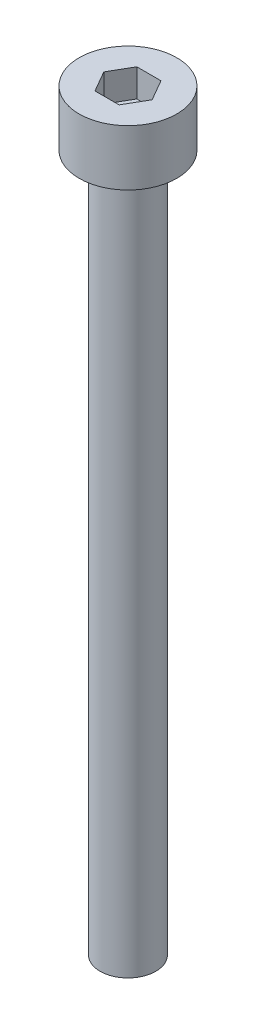
SolidWorks part; units mm, degrees
material "AISI 304"
ref_plane "前视基准面" through (0, 0, 0) normal (0, 0, 1) x (1, 0, 0)
ref_plane "上视基准面" through (0, 0, 0) normal (0, 1, 0) x (1, 0, 0)
ref_plane "右视基准面" through (0, 0, 0) normal (1, 0, 0) x (0, 0, -1)
sketch "草图1" plane through (0, 0, 0) normal (0, 1, 0) x (1, 0, 0)
  circle A0 centre (0, 0) radius 3.5
  dimension "D1" = 7
extrude "杯头" add sketch "草图1" along normal blind 4
sketch "草图2" plane through (0, 4, 0) normal (0, 1, 0) x (1, 0, 0)
  line L1 (1.7321, 0) -> (0.866, 1.5)
  line L2 (0.866, 1.5) -> (-0.866, 1.5)
  line L3 (-0.866, 1.5) -> (-1.7321, 0)
  line L4 (-1.7321, 0) -> (-0.866, -1.5)
  line L5 (-0.866, -1.5) -> (0.866, -1.5)
  line L6 (0.866, -1.5) -> (1.7321, 0)
  circle A0 centre (0, 0) radius 1.5 construction
  dimension "D1" = 3
extrude "内六角口" cut sketch "草图2" against normal blind 2
sketch "草图3" plane through (0, 0, 0) normal (0, -1, 0) x (1, 0, 0)
  circle A0 centre (0, 0) radius 2
  dimension "D1" = 4
extrude "螺纹长度" add sketch "草图3" along normal blind 50
